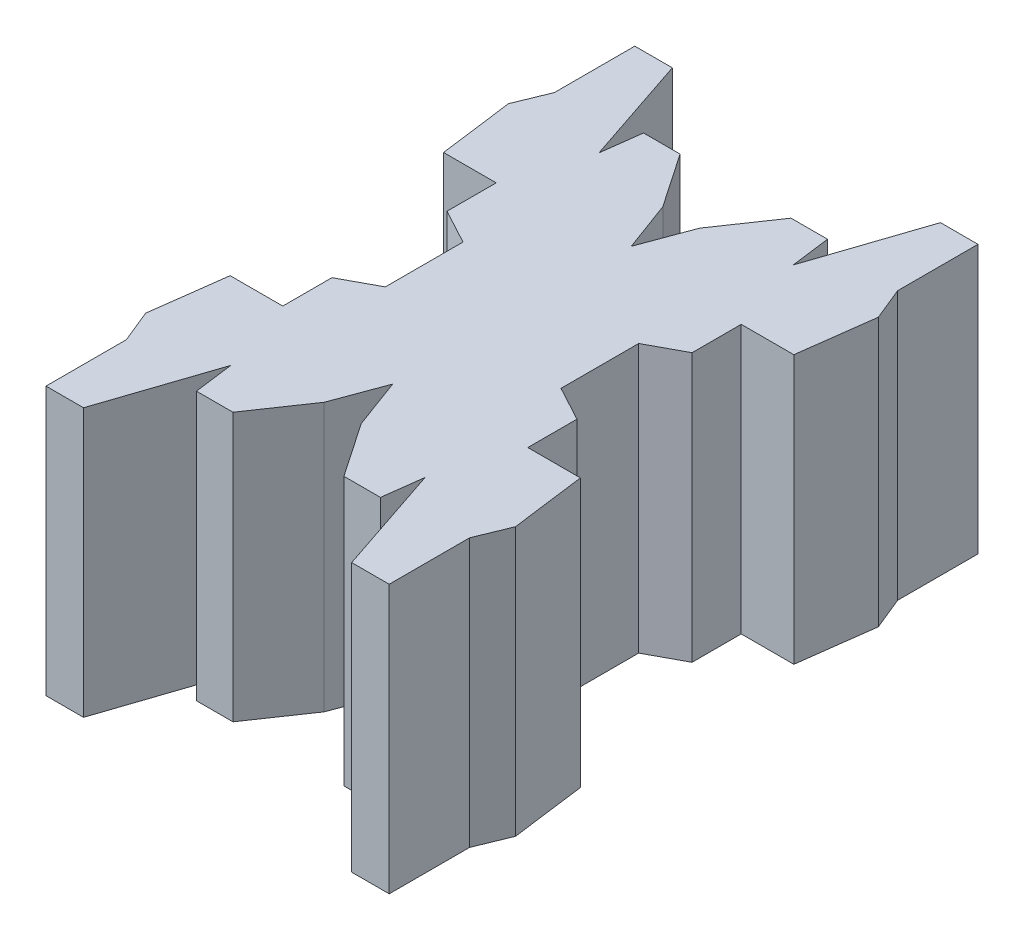
SolidWorks part; units mm, degrees
ref_plane "Front Plane" through (0, 0, 0) normal (0, 0, 1) x (1, 0, 0)
ref_plane "Top Plane" through (0, 0, 0) normal (0, 1, 0) x (1, 0, 0)
ref_plane "Right Plane" through (0, 0, 0) normal (1, 0, 0) x (0, 0, -1)
sketch "Sketch1" plane through (0, 0, 0) normal (0, 1, 0) x (1, 0, 0)
  line L0 (157.2098, 585.4355) -> (729.1227, 575.4527) construction
  line L1 (39.2599, 54.5962) -> (39.2599, 44.6062) construction
  line L2 (24.7599, 17.7624) -> (28.7599, 29.7023)
  line L3 (41.2599, 31.2936) -> (39.2599, 36.7023)
  line L4 (29.7599, 53.803) -> (29.7599, 45.3993)
  line L5 (29.7599, 45.3993) -> (26.0099, 43.3778)
  line L6 (58.2006, 38.0614) -> (52.5099, 38.0614)
  line L7 (20.3192, 38.0614) -> (19.2599, 29.9809)
  line L8 (39.2599, 49.6012) -> (29.7599, 49.6012) construction
  line L9 (45.2599, 25.4238) -> (41.2599, 31.2936)
  line L10 (26.0099, 43.3778) -> (26.0099, 38.0614)
  line L11 (49.2119, 25.4238) -> (45.2599, 25.4238)
  line L12 (49.7599, 29.7023) -> (49.2119, 25.4238)
  line L13 (24.7599, 17.7624) -> (20.7014, 17.7624)
  line L14 (57.8183, 26.4576) -> (57.8183, 17.7624)
  line L15 (59.2599, 29.9809) -> (57.8183, 26.4576)
  line L16 (49.2119, 25.4238) -> (45.2599, 25.4238)
  line L17 (29.3078, 25.4238) -> (33.2599, 25.4238)
  line L18 (53.7599, 17.7624) -> (57.8183, 17.7624)
  line L19 (52.5099, 43.3778) -> (52.5099, 38.0614)
  line L20 (58.2006, 38.0614) -> (59.2599, 29.9809)
  line L22 (48.7599, 45.3993) -> (52.5099, 43.3778)
  line L23 (19.2599, 29.9809) -> (20.7014, 26.4576)
  line L24 (20.7014, 26.4576) -> (20.7014, 17.7624)
  line L25 (28.7599, 29.7023) -> (29.3078, 25.4238)
  line L26 (29.3078, 25.4238) -> (33.2599, 25.4238)
  line L27 (33.2599, 25.4238) -> (37.2599, 31.2936)
  line L28 (37.2599, 31.2936) -> (39.2599, 36.7023)
  line L29 (48.7599, 53.803) -> (48.7599, 45.3993)
  line L30 (53.7599, 17.7624) -> (49.7599, 29.7023)
  line L31 (53.7599, 81.4399) -> (49.7599, 69.5)
  line L32 (37.2599, 67.9088) -> (39.2599, 62.5)
  line L33 (33.2599, 73.7785) -> (37.2599, 67.9088)
  line L34 (29.3078, 73.7785) -> (33.2599, 73.7785)
  line L35 (28.7599, 69.5) -> (29.3078, 73.7785)
  line L36 (20.7014, 72.7447) -> (20.7014, 81.4399)
  line L37 (19.2599, 69.2214) -> (20.7014, 72.7447)
  line L38 (48.7599, 53.803) -> (52.5099, 55.8246)
  line L40 (58.2006, 61.1409) -> (59.2599, 69.2214)
  line L41 (52.5099, 55.8246) -> (52.5099, 61.1409)
  line L42 (53.7599, 81.4399) -> (57.8183, 81.4399)
  line L43 (29.3078, 73.7785) -> (33.2599, 73.7785)
  line L44 (49.2119, 73.7785) -> (45.2599, 73.7785)
  line L45 (59.2599, 69.2214) -> (57.8183, 72.7447)
  line L46 (57.8183, 72.7447) -> (57.8183, 81.4399)
  line L47 (24.7599, 81.4399) -> (20.7014, 81.4399)
  line L48 (49.7599, 69.5) -> (49.2119, 73.7785)
  line L49 (49.2119, 73.7785) -> (45.2599, 73.7785)
  line L50 (26.0099, 55.8246) -> (26.0099, 61.1409)
  line L51 (45.2599, 73.7785) -> (41.2599, 67.9088)
  line L52 (20.3192, 61.1409) -> (19.2599, 69.2214)
  line L54 (29.7599, 53.803) -> (26.0099, 55.8246)
  line L55 (41.2599, 67.9088) -> (39.2599, 62.5)
  line L56 (24.7599, 81.4399) -> (28.7599, 69.5)
  line L57 (20.3192, 38.0614) -> (26.0099, 38.0614)
  line L58 (20.3192, 61.1409) -> (26.0099, 61.1409)
  line L59 (58.2006, 61.1409) -> (52.5099, 61.1409)
  point P35 (48.7599, 49.6012)
  dimension "D6" = 9.5
  dimension "D8" = 7
  dimension "D9" = 7.9038
extrude "Boss-Extrude1" add sketch "Sketch1" along normal blind 29
